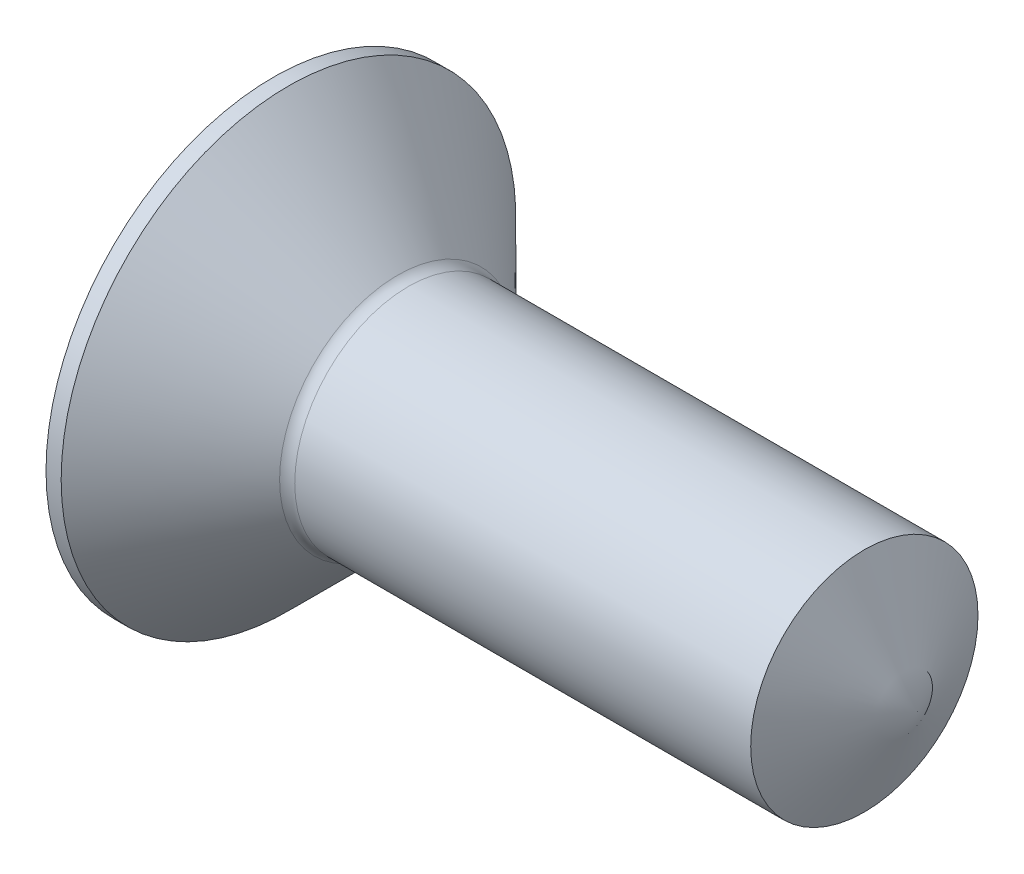
SolidWorks part; units mm, degrees
ref_plane "Front" through (0, 0, 0) normal (0, 0, 1) x (1, 0, 0)
ref_plane "Top" through (0, 0, 0) normal (0, 1, 0) x (1, 0, 0)
ref_plane "Right" through (0, 0, 0) normal (1, 0, 0) x (0, 0, -1)
sketch "Sketch1" plane through (0, 0, 0) normal (0, 1, 0) x (1, 0, 0)
  line L0 (-6.5065, 0) -> (5.6973, 0) construction
  line L1 (1.7, 1.5) -> (8.5, 1.5)
  line L2 (1.7, 1.5) -> (0.2, 3)
  line L3 (0.2, 3) -> (0, 3)
  line L4 (0, 3) -> (0, 0)
  line L5 (8.5, 1.5) -> (8.5, 0)
  line L6 (8.5, 0) -> (0, 0)
  dimension "D1" = 45
  dimension "d" = 3
  dimension "dk" = 6
  dimension "l" = 8.5
  dimension "k" = 1.7
revolve "Base" add sketch "Sketch1" angle 360 about L0
cosmetic thread "ThreadCosmetic1" parameters "D1"=3.5, "D2"=2.75
sketch "Sketch3" plane through (0, 0, 0) normal (0, 0, 1) x (1, 0, 0)
  line L0 (4.8835, 0) -> (6.2249, 0) construction
  line L2 (8.6576, 0) -> (8.6576, 20)
  line L3 (8.6576, 20) -> (-0.8262, 20)
  line L4 (-0.8262, 20) -> (8.5, 0)
  line L5 (8.5, 0) -> (8.6576, 0)
  line L7 (8.5, -1.5) -> (8.5, 1.5) construction
  dimension "D1" = 65
  dimension "D2" = 20
  dimension "D3" = 0.1576
revolve "Cut-Revolve1" cut sketch "Sketch3" angle 360 about L0
fillet "Fillet2" radius 0.2 1 edges at (1.7, 0, 1.5)
ref_plane "Plane1" through (1.95, 0, 0) normal (-1, 0, 0) x (0, 0, 1)
sketch "Sketch2" plane through (0, -0.6808, 0.3068) normal (-1, 0, 0) x (0, 0, 1)
  line L0 (-2.7047, 0.6808) -> (2.0912, 0.6808) construction
  line L1 (-0.3068, 2.3397) -> (-0.3068, -2.278) construction
  line L2 (-0.6868, 1.0608) -> (-2.2068, 1.0608)
  line L3 (0.0732, -1.2192) -> (-0.6868, -1.2192)
  line L4 (0.0732, -1.2192) -> (0.0732, 0.3008)
  line L5 (0.0732, 2.5808) -> (-0.6868, 2.5808)
  line L6 (-0.6868, -1.2192) -> (-0.6868, 0.3008)
  line L7 (1.5932, 1.0608) -> (0.0732, 1.0608)
  line L8 (1.5932, 1.0608) -> (1.5932, 0.3008)
  line L9 (1.5932, 0.3008) -> (0.0732, 0.3008)
  line L10 (-2.2068, 1.0608) -> (-2.2068, 0.3008)
  line L11 (-0.6868, 0.3008) -> (-2.2068, 0.3008)
  line L12 (-0.6868, 1.0608) -> (-0.6868, 2.5808)
  line L13 (0.0732, 1.0608) -> (0.0732, 2.5808)
  point P19 (-0.6868, 1.0608)
  point P24 (0.0732, 1.0608)
  dimension "D1" = 0.76
  dimension "m" = 3.8
  dimension "D2" = 3.8
  dimension "D3" = 0.76
sketch "Sketch4" plane through (1.95, 0, 0) normal (-1, 0, 0) x (0, 0, 1)
  point P0 (0, 0)
loft "Cut-Loft1" cut profiles "Sketch2", "Sketch4"
sketch "Sketch5" plane through (0, 0, 0) normal (0, 0, 1) x (1, 0, 0)
  line L0 (3.5, 1.7) -> (3.625, 1.7)
  line L1 (3.625, 1.7) -> (3.625, 1.5)
  line L2 (3.625, 1.5) -> (3.5625, 1.3917)
  line L3 (3.5, 1.5) -> (3.5625, 1.3917)
  line L4 (3.5, 1.7) -> (3.5, 1.5)
  line L5 (10.7743, 0) -> (0, 0) construction
  line L6 (3.5, 1.5) -> (3.625, 1.5) construction
  line L7 (3.5625, 1.5) -> (3.5625, 1.3917) construction
  line L8 (7.8005, 1.5) -> (1.7828, 1.5) construction
  point P5 (3.5625, 1.7)
  dimension "D1" = 0.2
  dimension "D2" = 0.125
  dimension "D3" = 5
revolve "Cut-Revolve10" [suppressed] cut sketch "Sketch5" angle 360 about L5
pattern_linear "LPattern10" [suppressed] count 20 spacing 0.25 along (1, 0, 0)
equation "\"D2@Sketch2\" = \"m@Sketch2\""
equation "\"D3@Sketch2\" = \"D1@Sketch2\""
equation "\"D1@Sketch2\" = \"m@Sketch2\" / 5"
equation "\"D1@Plane1\" = \"k@Sketch1\" + 0.25"
equation "\"D2@Sketch5\" =  ( \"d@Sketch1\" - \"D2@ThreadCosmetic1\" )  / 2"
equation "\"D3@Sketch5\" = \"D1@ThreadCosmetic1\" + \"d@Sketch1\" / 2"
equation "\"D3@LPattern10\" =\"D2@Sketch5\"* 2"
equation "\"D1@LPattern10\" = \"D3@Sketch5\" / \"D3@LPattern10\""
